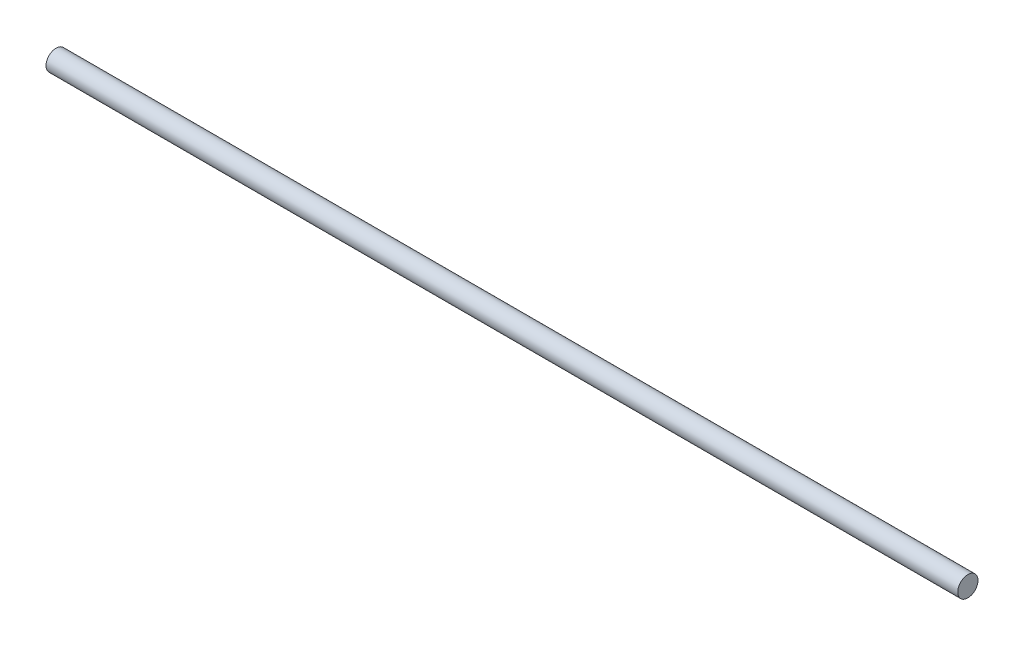
SolidWorks part; units mm, degrees
material "6061-T6 (SS)"
ref_plane "Front Plane" through (0, 0, 0) normal (0, 0, 1) x (1, 0, 0)
ref_plane "Top Plane" through (0, 0, 0) normal (0, 1, 0) x (1, 0, 0)
ref_plane "Right Plane" through (0, 0, 0) normal (1, 0, 0) x (0, 0, -1)
sketch "Sketch1" plane through (0, 0, 0) normal (1, 0, 0) x (0, 0, -1)
  circle A0 centre (0, 0) radius 6.35
  dimension "D1" = 12.7
extrude "Boss-Extrude1" add sketch "Sketch1" along normal blind 571.5
